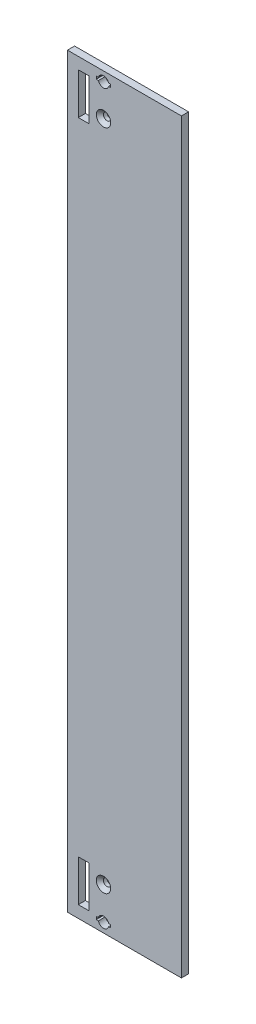
SolidWorks part; units mm, degrees
ref_plane "Front Plane" through (0, 0, 0) normal (0, 0, 1) x (1, 0, 0)
ref_plane "Top Plane" through (0, 0, 0) normal (0, 1, 0) x (1, 0, 0)
ref_plane "Right Plane" through (0, 0, 0) normal (1, 0, 0) x (0, 0, -1)
sketch "Sketch1" plane through (0, 0, 0) normal (0, 0, 1) x (1, 0, 0)
  line L0 (3.8, 262) -> (3.8, 0) construction
  line L1 (0, 0) -> (40, 0)
  line L2 (0, 0) -> (0, 262)
  line L3 (0, 262) -> (40, 262)
  line L4 (40, 0) -> (40, 262)
  line L5 (7.6, 262) -> (7.6, 0) construction
  line L6 (40, 4.2) -> (0, 4.2) construction
  line L7 (40, 257.95) -> (0, 257.95) construction
  line L8 (40, 18.75) -> (0, 18.75) construction
  line L9 (0, 243.4) -> (40, 243.4) construction
  line L10 (12.65, 262) -> (12.65, 0) construction
  line L11 (3.8, 257.95) -> (7.6, 257.95)
  line L12 (3.8, 257.95) -> (3.8, 243.4)
  line L13 (3.8, 243.4) -> (7.6, 243.4)
  line L14 (7.6, 257.95) -> (7.6, 243.4)
  line L15 (3.8, 18.75) -> (7.6, 18.75)
  line L16 (3.8, 18.75) -> (3.8, 4.2)
  line L17 (3.8, 4.2) -> (7.6, 4.2)
  line L18 (7.6, 18.75) -> (7.6, 4.2)
  line L19 (10.8585, 3.8) -> (10.1085, 3.8)
  line L20 (10.1085, 3.8) -> (10.1085, 2.8)
  line L21 (10.1085, 2.8) -> (10.8585, 2.8)
  line L22 (14.4415, 2.8) -> (15.1915, 2.8)
  line L23 (15.1915, 2.8) -> (15.1915, 3.8)
  line L24 (15.1915, 3.8) -> (14.4415, 3.8)
  line L25 (10.8585, 259.2) -> (10.1085, 259.2)
  line L26 (10.1085, 258.2) -> (10.8585, 258.2)
  line L27 (10.1085, 259.2) -> (10.1085, 258.2)
  line L28 (14.4415, 258.2) -> (15.1915, 258.2)
  line L29 (15.1915, 258.2) -> (15.1915, 259.2)
  line L30 (15.1915, 259.2) -> (14.4415, 259.2)
  circle A0 centre (12.65, 258.7) radius 1.86 construction
  circle A1 centre (12.65, 3.3) radius 1.86 construction
  circle A2 centre (12.65, 247.5) radius 1.28
  circle A3 centre (12.65, 14.75) radius 1.28
  arc A4 (10.8585, 3.8) -> (14.4415, 3.8) centre (12.65, 3.3) cw
  arc A5 (10.8585, 2.8) -> (14.4415, 2.8) centre (12.65, 3.3) ccw
  circle A6 centre (12.65, 258.7) radius 1.86 construction
  arc A7 (10.8585, 259.2) -> (14.4415, 259.2) centre (12.65, 258.7) cw
  arc A8 (10.8585, 258.2) -> (14.4415, 258.2) centre (12.65, 258.7) ccw
extrude "Boss-Extrude1" add sketch "Sketch1" along normal blind 2.5
chamfer "Chamfer1" distance 1.25 angle 45 1 edges at (13.93, 247.5, 2.5)
chamfer "Chamfer2" distance 1.25 angle 45 1 edges at (13.93, 14.75, 2.5)
